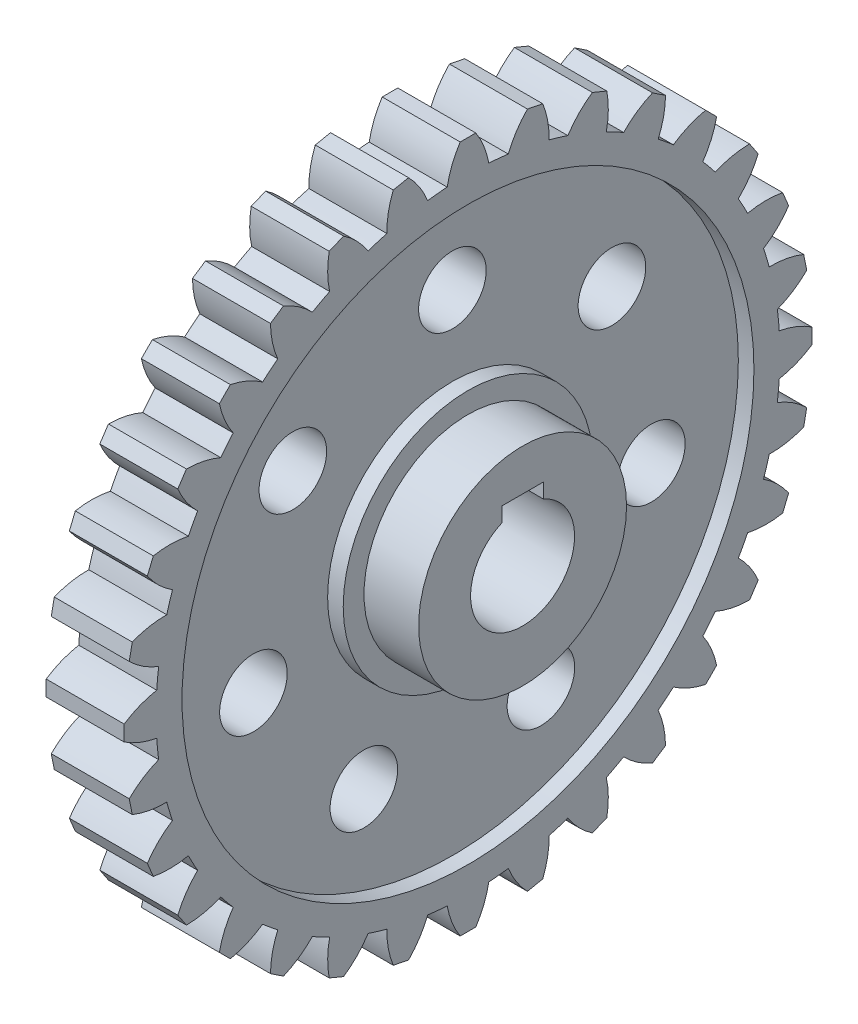
SolidWorks part; units mm, degrees
ref_plane "Front Plane" through (0, 0, 0) normal (0, 0, 1) x (1, 0, 0)
ref_plane "Top Plane" through (0, 0, 0) normal (0, 1, 0) x (1, 0, 0)
ref_plane "Right Plane" through (0, 0, 0) normal (1, 0, 0) x (0, 0, -1)
sketch "Sketch1" plane through (0, 0, 0) normal (1, 0, 0) x (0, 0, -1)
  circle A0 centre (0, 0) radius 60
  dimension "D1" = 120
extrude "Boss-Extrude1" add sketch "Sketch1" along normal mid plane 15
sketch "Sketch2" plane through (7.5, 0, 0) normal (1, 0, 0) x (0, 0, -1)
  line L0 (0, 0) -> (0, 66.1335) construction
  line L1 (-1.5, 66.1335) -> (1.5, 66.1335)
  arc A0 (-4, 59.8665) -> (4, 59.8665) centre (0, 0) cw
  circle A1 centre (0, 0) radius 60 construction
  arc A2 (-4, 59.8665) -> (-1.5, 66.1335) centre (12.726, 56.8264) cw
  arc A3 (4, 59.8665) -> (1.5, 66.1335) centre (-12.726, 56.8264) ccw
  point P9 (0, 60)
  dimension "D4" = 17
  dimension "D1" = 1.5
  dimension "D2" = 6.267
  dimension "D3" = 4
extrude "Boss-Extrude2" add sketch "Sketch2" against normal up to surface (15 mm away) up to face at (-7.5, 0, -60)
pattern_circular "CirPattern1" count 32 over 360 about axis through (0, 0, 0) along (1, 0, 0) of "Boss-Extrude2"
sketch "Sketch4" plane through (0, 0, 0) normal (1, 0, 0) x (0, 0, -1)
  circle A0 centre (0, 0) radius 20
  dimension "D1" = 40
extrude "Boss-Extrude4" add sketch "Sketch4" along normal mid plane 36
sketch "Sketch5" plane through (18, 0, 0) normal (1, 0, 0) x (0, 0, -1)
  line L0 (0, 0) -> (0, 12) construction
  line L1 (-4, 12) -> (4, 12)
  line L2 (-4, 12) -> (-4, 9.1652)
  line L3 (4, 12) -> (4, 9.1652)
  arc A0 (-4, 9.1652) -> (4, 9.1652) centre (0, 0) ccw
  dimension "D1" = 20
  dimension "D2" = 12
  dimension "D3" = 8
extrude "Cut-Extrude1" cut sketch "Sketch5" against normal through all
sketch "Sketch6" plane through (7.5, 0, 0) normal (1, 0, 0) x (0, 0, -1)
  circle A0 centre (0, 0) radius 24
  circle A1 centre (0, 0) radius 55
  dimension "D1" = 110
  dimension "D2" = 48
extrude "Cut-Extrude2" cut sketch "Sketch6" against normal blind 3
sketch "Sketch7" plane through (4.5, 0, 0) normal (1, 0, 0) x (0, 0, -1)
  circle A0 centre (0, 0) radius 39.25 construction
  circle A1 centre (0, 39.25) radius 6.5
  circle A2 centre (30.6869, 24.472) radius 6.5
  circle A3 centre (38.2659, -8.7339) radius 6.5
  circle A4 centre (17.0299, -35.363) radius 6.5
  circle A5 centre (-17.0299, -35.363) radius 6.5
  circle A6 centre (-38.2659, -8.7339) radius 6.5
  circle A7 centre (-30.6869, 24.472) radius 6.5
  point P19 (0, 0)
  dimension "D1" = 78.5
  dimension "D2" = 13
  dimension "D3" = 7
extrude "Cut-Extrude3" cut sketch "Sketch7" against normal through all
